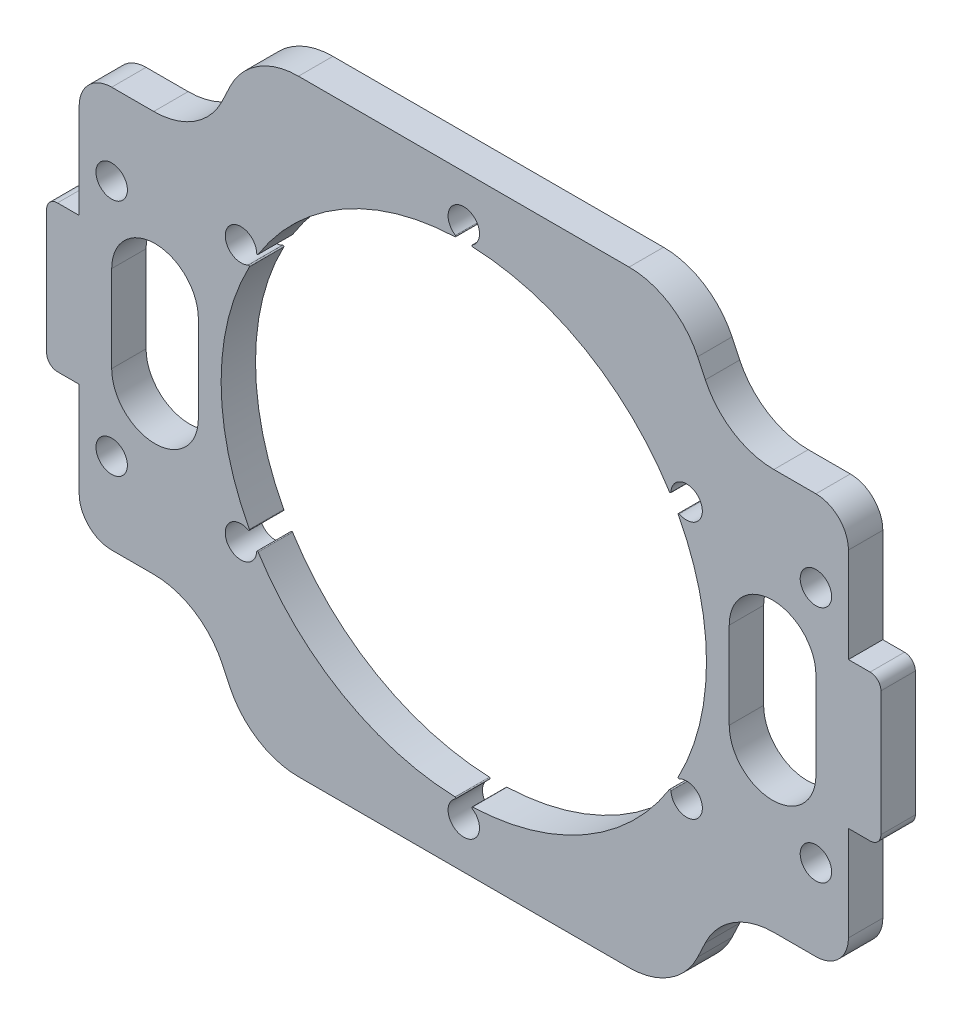
SolidWorks part; units mm, degrees
material "AISI 1035 Steel (SS)"
ref_plane "Front Plane" through (0, 0, 0) normal (0, 0, 1) x (1, 0, 0)
ref_plane "Top Plane" through (0, 0, 0) normal (0, 1, 0) x (1, 0, 0)
ref_plane "Right Plane" through (0, 0, 0) normal (1, 0, 0) x (0, 0, -1)
sketch "Sketch1" plane through (0, 0, 0) normal (0, 0, 1) x (1, 0, 0)
  line L1 (-35.5, 28) -> (35.5, 28)
  line L2 (-35.5, 28) -> (-35.5, -28)
  line L3 (-35.5, -28) -> (35.5, -28)
  line L4 (35.5, 28) -> (35.5, -28)
  line L5 (-35.5, 28) -> (35.5, -28) construction
  line L6 (-35.5, -28) -> (35.5, 28) construction
  circle A0 centre (0, 0) radius 22.4
  point P0 (0, 0)
  dimension "D3" = 44.8
  dimension "D1" = 56
  dimension "14" = 71
extrude "Boss-Extrude1" add sketch "Sketch1" along normal blind 3.175
sketch "Sketch3" plane through (0, 0, 3.175) normal (0, 0, 1) x (1, 0, 0)
  circle A0 centre (0, 0) radius 23.75 construction
  circle A1 centre (0, 23.75) radius 1.45
  circle A2 centre (20.5681, 11.875) radius 1.45
  circle A3 centre (20.5681, -11.875) radius 1.45
  circle A4 centre (0, -23.75) radius 1.45
  circle A5 centre (-20.5681, -11.875) radius 1.45
  circle A6 centre (-20.5681, 11.875) radius 1.45
  point P18 (0, 0)
  dimension "D1" = 2.9
  dimension "D3" = 47.5
  dimension "D2" = 6
extrude "Cut-Extrude2" cut sketch "Sketch3" against normal through all
sketch "Sketch11" plane through (0, 0, 3.175) normal (0, 0, 1) x (1, 0, 0)
  line L1 (35.5, 28) -> (-35.5, 28) construction
  line L2 (-24.188, 18.5) -> (-35.5, 18.5)
  line L3 (-35.5, 28) -> (-35.5, -28) construction
  line L4 (-35.5, 18.5) -> (-35.5, 28)
  line L5 (-35.5, 28) -> (-19.688, 28)
  line L6 (0, 39.643) -> (0, -36.5597) construction
  line L7 (35.5, 28) -> (19.688, 28)
  line L8 (35.5, 18.5) -> (35.5, 28)
  line L9 (24.188, 18.5) -> (35.5, 18.5)
  line L10 (19.688, 28) -> (24.188, 18.5)
  line L11 (-5.9465, 0) -> (11.012, 0) construction
  line L12 (19.688, -28) -> (24.188, -18.5)
  line L13 (24.188, -18.5) -> (35.5, -18.5)
  line L14 (35.5, -18.5) -> (35.5, -28)
  line L15 (35.5, -28) -> (19.688, -28)
  line L16 (-35.5, -28) -> (-19.688, -28)
  line L17 (-35.5, -18.5) -> (-35.5, -28)
  line L18 (-24.188, -18.5) -> (-35.5, -18.5)
  line L19 (-19.688, -28) -> (-24.188, -18.5)
  line L20 (-24.188, 18.5) -> (-19.688, 28)
  dimension "D1" = 4.5
  dimension "D2" = 37
extrude "Cut-Extrude7" cut sketch "Sketch11" against normal through all
sketch "Sketch12" plane through (0, 0, 3.175) normal (0, 0, 1) x (1, 0, 0)
  line L0 (0, 16.2679) -> (0, -10.1222) construction
  line L1 (-32.5, 11) -> (-32.5, -11) construction
  line L2 (-35.5, 18.5) -> (-35.5, -18.5) construction
  circle A0 centre (-32.5, 11) radius 1.45
  circle A1 centre (-32.5, -11) radius 1.45
  circle A2 centre (32.5, -11) radius 1.45
  circle A3 centre (32.5, 11) radius 1.45
  point P5 (-32.5, 0)
  dimension "D2" = 2.9
  dimension "D1" = 22
  dimension "D3" = 3
extrude "Cut-Extrude8" cut sketch "Sketch12" against normal through all both and the other way through all
sketch "Sketch15" plane through (0, 0, 0) normal (0, 0, -1) x (-1, 0, 0)
  line L0 (0, 37.4812) -> (0, -9.8909) construction
  line L1 (-35.5, -18.5) -> (-35.5, 18.5) construction
  line L2 (-38.5, 6.75) -> (-35.5, 6.75)
  line L3 (-38.5, 6.75) -> (-38.5, -6.75)
  line L4 (-38.5, -6.75) -> (-35.5, -6.75)
  line L5 (-35.5, 6.75) -> (-35.5, -6.75)
  line L6 (35.5, 6.75) -> (35.5, -6.75)
  line L7 (38.5, -6.75) -> (35.5, -6.75)
  line L8 (38.5, 6.75) -> (38.5, -6.75)
  line L9 (38.5, 6.75) -> (35.5, 6.75)
  point P9 (-35.5, 0)
  dimension "D1" = 3
  dimension "D2" = 13.5
extrude "Boss-Extrude3" add sketch "Sketch15" against normal up to surface (3.175 mm away) up to face at (33.95, 11, 3.175)
fillet "Fillet3" radius 7 8 edges at (19.688, -28, 1.5875) (24.188, -18.5, 1.5875) (-19.688, -28, 1.5875) (-24.188, -18.5, 1.5875) (19.688, 28, 1.5875) (24.188, 18.5, 1.5875) (-19.688, 28, 1.5875) (-24.188, 18.5, 1.5875)
fillet "Fillet4" radius 3 4 edges at (35.5, -18.5, 1.5875) (35.5, 18.5, 1.5875) (-35.5, 18.5, 1.5875) (-35.5, -18.5, 1.5875)
sketch "Sketch10" plane through (0, 0, 3.175) normal (0, 0, 1) x (1, 0, 0)
  line L0 (-28.5, 4) -> (-28.5, -4) construction
  line L1 (-24.5, 4) -> (-24.5, -4)
  line L2 (-32.5, 4) -> (-32.5, -4)
  line L3 (0, 38.1014) -> (0, -40.9645) construction
  line L4 (28.5, 4) -> (28.5, -4) construction
  line L5 (24.5, 4) -> (24.5, -4)
  line L6 (32.5, 4) -> (32.5, -4)
  arc A0 (-24.5, 4) -> (-32.5, 4) centre (-28.5, 4) ccw
  arc A1 (-32.5, -4) -> (-24.5, -4) centre (-28.5, -4) ccw
  arc A2 (24.5, 4) -> (32.5, 4) centre (28.5, 4) cw
  arc A3 (32.5, -4) -> (24.5, -4) centre (28.5, -4) cw
  point P2 (-28.5, 0)
  point P12 (28.5, 0)
  dimension "D1" = 8
  dimension "D2" = 32.5
  dimension "D3" = 8
extrude "Cut-Extrude6" cut sketch "Sketch10" against normal through all
fillet "Fillet5" radius 1 4 edges at (-38.5, -6.75, 1.5875) (-38.5, 6.75, 1.5875) (38.5, -6.75, 1.5875) (38.5, 6.75, 1.5875)
fillet "Fillet6" radius 0.075 12 edges at (19.1369, -11.6421, 1.5875) (19.6508, -10.752, 1.5875) (-0.5139, -22.3941, 1.5875) (0.5139, -22.3941, 1.5875) (-19.6508, -10.752, 1.5875) (-19.1369, -11.6421, 1.5875) (-19.1369, 11.6421, 1.5875) (-19.6508, 10.752, 1.5875) (0.5139, 22.3941, 1.5875) (-0.5139, 22.3941, 1.5875) (19.6508, 10.752, 1.5875) (19.1369, 11.6421, 1.5875)
